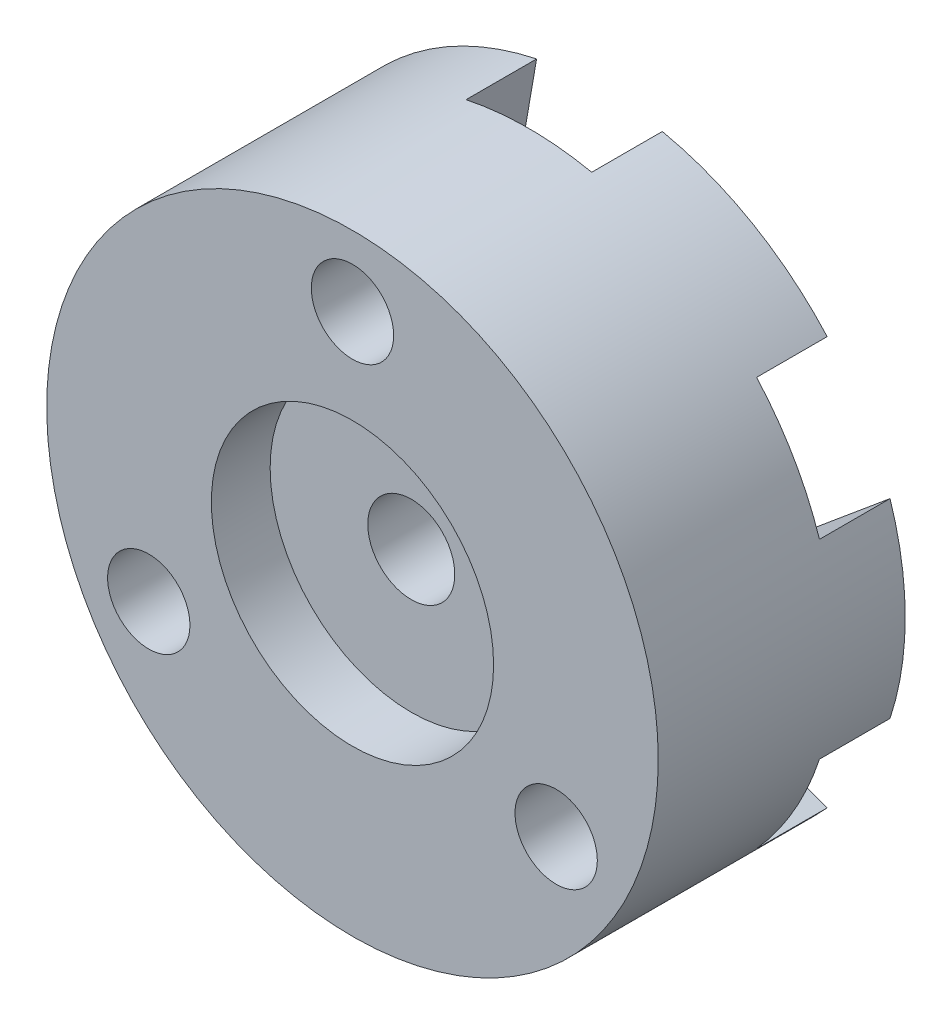
SolidWorks part; units mm, degrees
ref_plane "正面(Front)" through (0, 0, 0) normal (0, 0, 1) x (1, 0, 0)
ref_plane "平面(Top)" through (0, 0, 0) normal (0, 1, 0) x (1, 0, 0)
ref_plane "右側面(Right)" through (0, 0, 0) normal (1, 0, 0) x (0, 0, -1)
sketch "ｽｹｯﾁ1" plane through (0, 0, 0) normal (0, 0, 1) x (1, 0, 0)
  line L0 (0, 0) -> (0, 15.5568) construction
  line L1 (0, 0) -> (-3.75, 6.4952) construction
  line L2 (-3.75, 6.4952) -> (-2.4634, 13.9265)
  arc A0 (-2.4634, 13.9265) -> (0, 16) centre (0, 13.5) cw
  dimension "D1" = 2.5
  dimension "D2" = 30
  dimension "D3" = 16
  dimension "D4" = 7.5
sketch "ｽｹｯﾁ2" plane through (0, 0, 0) normal (0, 0, 1) x (1, 0, 0)
  line L0 (-3.75, 6.4952) -> (-2.4634, 13.9265) construction
  line L1 (-3.75, 6.4952) -> (-2.4634, 13.9265)
  line L2 (0, 0) -> (0, 19.5691) construction
  line L3 (3.75, 6.4952) -> (2.4634, 13.9265)
  line L4 (3.75, 6.4952) -> (10.829, 9.0966)
  line L5 (7.5, 0) -> (13.2924, 4.8299)
  line L6 (7.5, 0) -> (13.2924, -4.8299)
  line L7 (3.75, -6.4952) -> (10.829, -9.0966)
  line L8 (3.75, -6.4952) -> (2.4634, -13.9265)
  line L9 (-3.75, -6.4952) -> (-2.4634, -13.9265)
  line L10 (-3.75, -6.4952) -> (-10.829, -9.0966)
  line L11 (-7.5, 0) -> (-13.2924, -4.8299)
  line L12 (-7.5, 0) -> (-13.2924, 4.8299)
  line L13 (-3.75, 6.4952) -> (-10.829, 9.0966)
  arc A0 (0, 16) -> (-2.4634, 13.9265) centre (0, 13.5) ccw construction
  arc A1 (2.4634, 13.9265) -> (-2.4634, 13.9265) centre (0, 13.5) ccw
  arc A2 (13.2924, 4.8299) -> (10.829, 9.0966) centre (11.6913, 6.75) ccw
  arc A3 (10.829, -9.0966) -> (13.2924, -4.8299) centre (11.6913, -6.75) ccw
  arc A4 (-2.4634, -13.9265) -> (2.4634, -13.9265) centre (0, -13.5) ccw
  arc A5 (-13.2924, -4.8299) -> (-10.829, -9.0966) centre (-11.6913, -6.75) ccw
  arc A6 (-10.829, 9.0966) -> (-13.2924, 4.8299) centre (-11.6913, 6.75) ccw
  dimension "D1" = 6
sketch "ｽｹｯﾁ3" plane through (0, 0, 0) normal (0, 0, 1) x (1, 0, 0)
  circle A0 centre (0, 0) radius 13
  dimension "D1" = 26
extrude "ﾎﾞｽ - 押し出し1" add sketch "ｽｹｯﾁ3" along normal blind 7.5
sketch "ｽｹｯﾁ4" plane through (0, 0, 7.5) normal (0, 0, 1) x (1, 0, 0)
  line L0 (0, 0) -> (0, 15.5568) construction
  line L1 (0, 0) -> (0, 10) construction
  circle A0 centre (0, 10) radius 1.75
  circle A1 centre (8.6603, -5) radius 1.75
  circle A2 centre (-8.6603, -5) radius 1.75
  dimension "D2" = 3.5
  dimension "D4" = 10
  dimension "D3" = 3
extrude "ｶｯﾄ - 押し出し1" cut sketch "ｽｹｯﾁ4" against normal through all
sketch "ｽｹｯﾁ5" plane through (0, 0, 0) normal (0, 0, -1) x (-1, 0, 0)
  circle A0 centre (8.6603, -5) radius 2.8
  circle A1 centre (0, 10) radius 2.8
  circle A2 centre (-8.6603, -5) radius 2.8
  dimension "D1" = 5.6
extrude "ｶｯﾄ - 押し出し2" cut sketch "ｽｹｯﾁ5" against normal blind 2.6
sketch "ｽｹｯﾁ6" plane through (0, 0, 7.5) normal (0, 0, 1) x (1, 0, 0)
  circle A0 centre (0, 0) radius 6
  dimension "D1" = 12
extrude "ｶｯﾄ - 押し出し3" cut sketch "ｽｹｯﾁ6" against normal through all
sketch "ｽｹｯﾁ7" plane through (0, 0, 0) normal (0, 0, -1) x (-1, 0, 0)
  circle A0 centre (0, 10) radius 2.8 construction
  circle A1 centre (0, 0) radius 13
  circle A2 centre (0, 0) radius 13
  circle A3 centre (8.6603, -5) radius 2.8 construction
  circle A4 centre (-8.6603, -5) radius 2.8 construction
  circle A5 centre (0, 10) radius 2.8
  circle A6 centre (8.6603, -5) radius 2.8
  circle A7 centre (-8.6603, -5) radius 2.8
  dimension "D1" = 0
extrude "ﾎﾞｽ - 押し出し2" add sketch "ｽｹｯﾁ7" along normal blind 3
extrude "ｶｯﾄ - 押し出し4" cut sketch "ｽｹｯﾁ2" against normal through all
sketch "ｽｹｯﾁ8" plane through (0, 0, 0) normal (0, 0, -1) x (-1, 0, 0)
  circle A0 centre (0, 0) radius 1.85
  circle A1 centre (0, 0) radius 6 construction
  circle A2 centre (0, 0) radius 6
  dimension "D1" = 3.7
extrude "ﾎﾞｽ - 押し出し3" add sketch "ｽｹｯﾁ8" against normal blind 5
